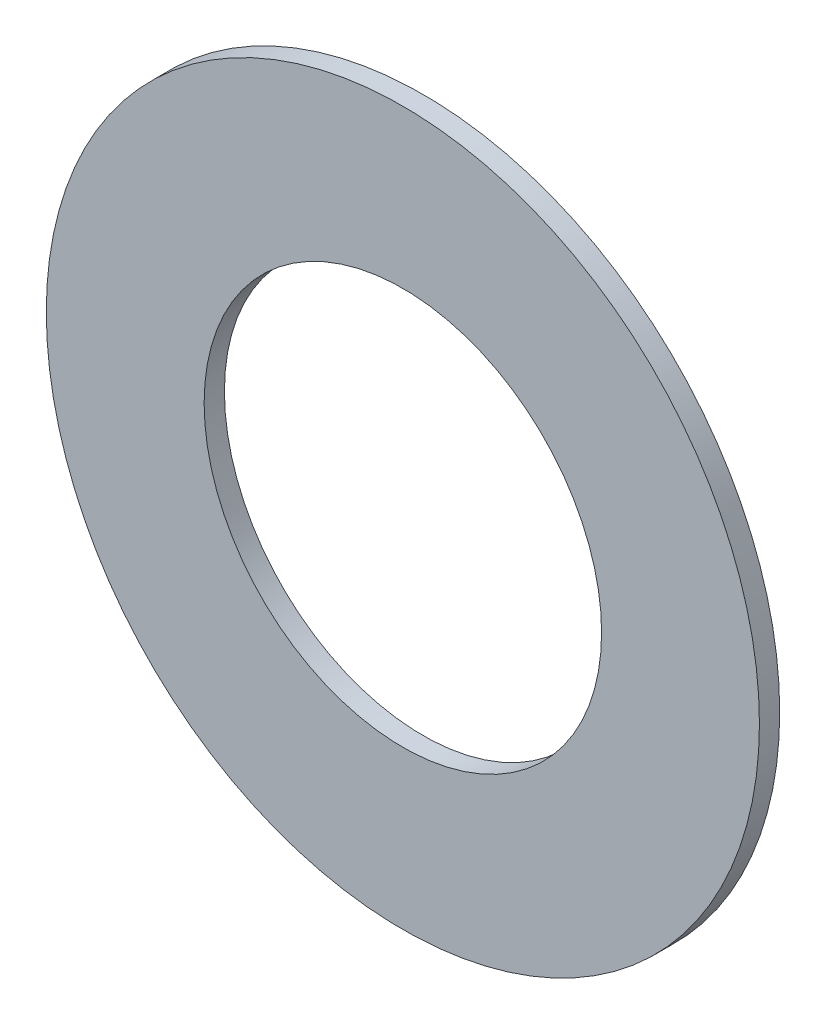
SolidWorks part; units mm, degrees
ref_plane "Front Plane" through (0, 0, 0) normal (0, 0, 1) x (1, 0, 0)
ref_plane "Top Plane" through (0, 0, 0) normal (0, 1, 0) x (1, 0, 0)
ref_plane "Right Plane" through (0, 0, 0) normal (1, 0, 0) x (0, 0, -1)
sketch "Sketch1" plane through (0, 0, 0) normal (0, 0, 1) x (1, 0, 0)
  line L0 (-7.9375, 0) -> (7.9375, 0) construction
  circle A0 centre (0, 0) radius 14.2875 construction
  circle A1 centre (0, 0) radius 7.9629 construction
  dimension "OD" = 28.575
  dimension "ID" = 15.9258
  dimension "For Shaft Diameter" = 15.875
sketch "Sketch2" plane through (0, 0, 0) normal (1, 0, 0) x (0, 0, -1)
  line L4 (0.4064, 14.2875) -> (-0.4064, 14.2875) construction
  point P0 (0, 14.2875)
  dimension "Thickness" = 0.8128
sketch "Sketch3" plane through (0, 0, 0) normal (0, 0, 1) x (1, 0, 0)
  circle A0 centre (0, 0) radius 7.9629 construction
  circle A1 centre (0, 0) radius 14.2875 construction
  circle A3 centre (0, 0) radius 7.9629
  circle A5 centre (0, 0) radius 14.2875
extrude "Boss-Extrude1" add sketch "Sketch3" against normal up to vertex (0.4064 mm away) and the other way up to vertex (0.4064 mm away)
equation "\"D1\"= \"Thickness@Sketch2\""
